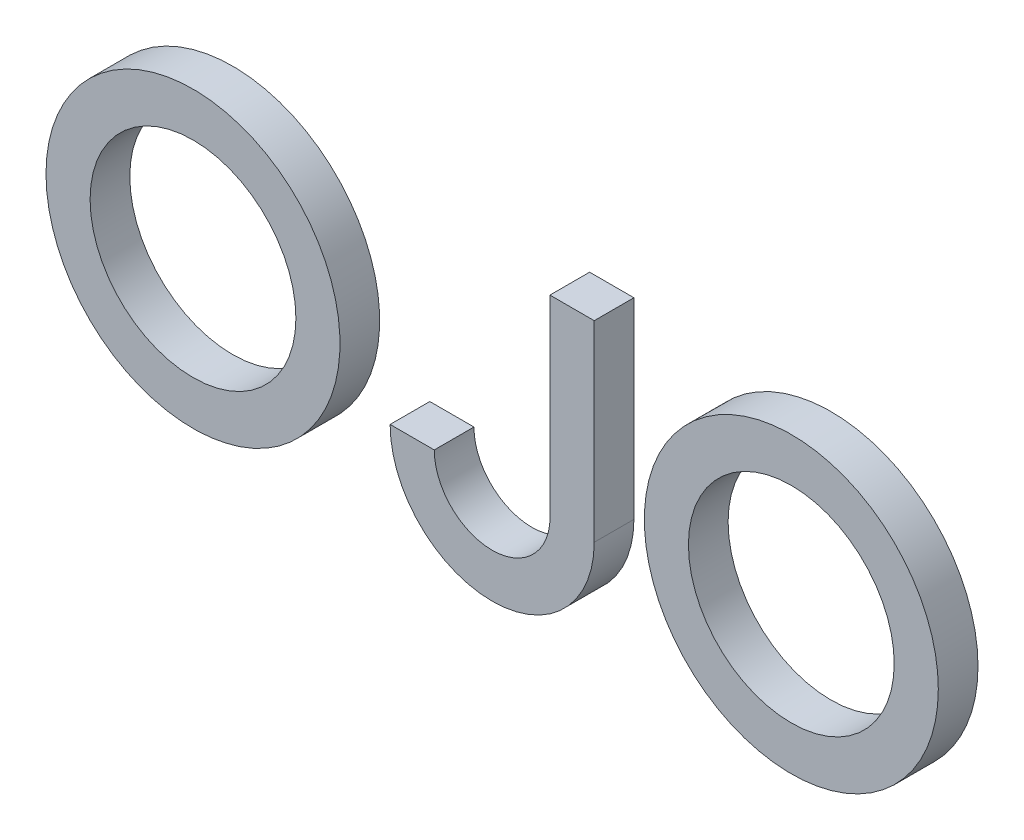
SolidWorks part; units mm, degrees
ref_plane "Ön Düzlem" through (0, 0, 0) normal (0, 0, 1) x (1, 0, 0)
ref_plane "Üst Düzlem" through (0, 0, 0) normal (0, 1, 0) x (1, 0, 0)
ref_plane "Sağ Düzlem" through (0, 0, 0) normal (1, 0, 0) x (0, 0, -1)
sketch "Sketch2" plane through (0, 0, 0) normal (0, 0, 1) x (1, 0, 0)
  line L0 (3.9304, 10) -> (6.944, 10)
  line L1 (6.944, 10) -> (6.944, -3.0569)
  line L2 (3.9304, 10) -> (3.941, -3.0538)
  line L3 (-6.9421, -3.0569) -> (-3.939, -3.0569)
  circle A0 centre (20.3518, 0) radius 7
  circle A1 centre (20.3518, 0) radius 10
  arc A2 (3.941, -3.0538) -> (-3.939, -3.0569) centre (0.001, -3.0569) cw
  arc A3 (6.944, -3.0569) -> (-6.9421, -3.0569) centre (0.001, -3.0569) cw
  circle A4 centre (-20.3518, 0) radius 10
  circle A5 centre (-20.3518, 0) radius 7
  point P13 (0.001, -8.4985)
  point P14 (0, 0)
extrude "Boss-Extrude1" add sketch "Sketch2" along normal blind 2.7
